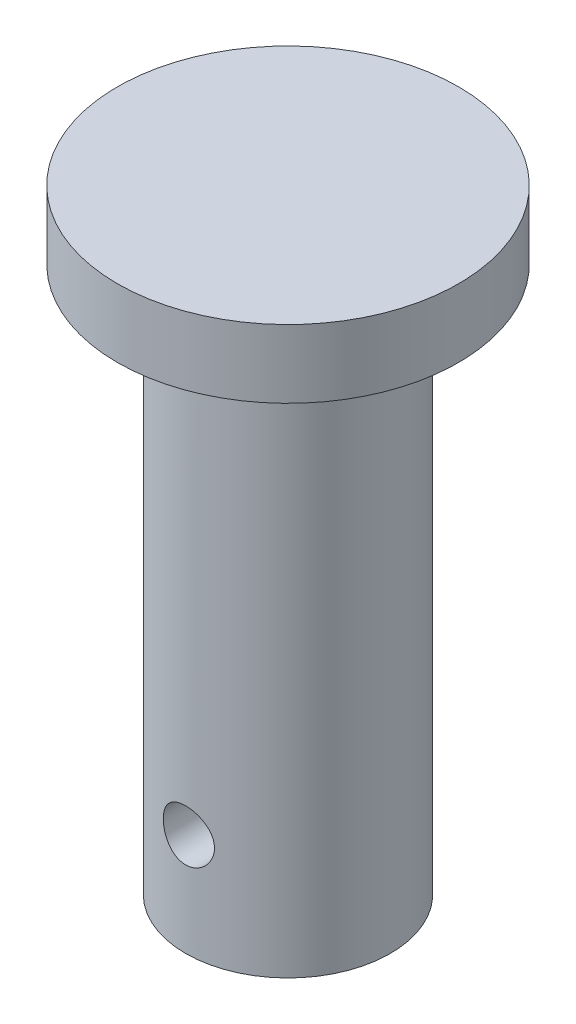
SolidWorks part; units mm, degrees
material "Stainless Steel (ferritic)"
ref_plane "Front Plane" through (0, 0, 0) normal (0, 0, 1) x (1, 0, 0)
ref_plane "Top Plane" through (0, 0, 0) normal (0, 1, 0) x (1, 0, 0)
ref_plane "Right Plane" through (0, 0, 0) normal (1, 0, 0) x (0, 0, -1)
sketch "Sketch1" plane through (0, 0, 0) normal (0, 0, 1) x (1, 0, 0)
  line L0 (0, 0) -> (6, 0)
  line L1 (6, 0) -> (6, 32)
  line L2 (6, 32) -> (10, 32)
  line L3 (10, 32) -> (10, 36)
  line L4 (10, 36) -> (0, 36)
  line L5 (0, 36) -> (0, 0)
  dimension "D1" = 32
  dimension "D2" = 6
  dimension "D3" = 10
  dimension "D4" = 4
revolve "Revolve1" add sketch "Sketch1" angle 360 about L5
sketch "Sketch2" plane through (0, 0, 0) normal (0, 0, 1) x (1, 0, 0)
  line L0 (-6, 32) -> (6, 32) construction
  circle A0 centre (0, 6) radius 1.5
  dimension "D1" = 3
  dimension "D2" = 26
extrude "Cut-Extrude1" cut sketch "Sketch2" against normal mid plane 14 contours A0
